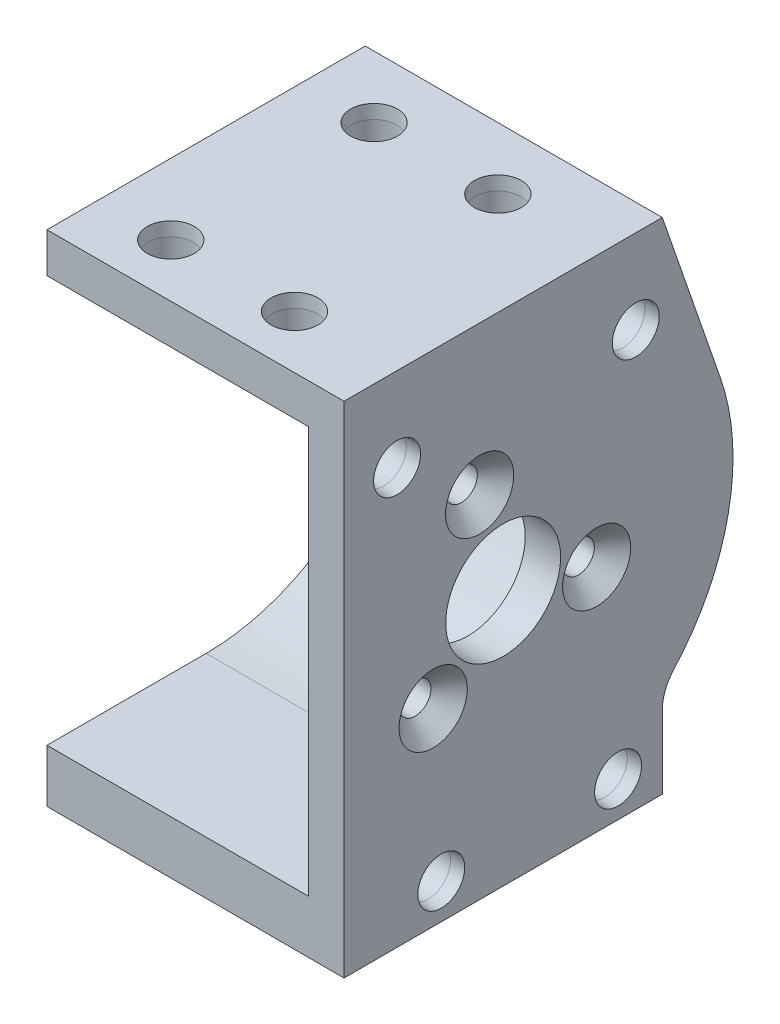
SolidWorks part; units mm, degrees
material "6061 Alloy"
ref_plane "Front Plane" through (0, 0, 0) normal (0, 0, 1) x (1, 0, 0)
ref_plane "Top Plane" through (0, 0, 0) normal (0, 1, 0) x (1, 0, 0)
ref_plane "Right Plane" through (0, 0, 0) normal (1, 0, 0) x (0, 0, -1)
ref_plane "Motor Face w/ 1.5mm tolerance" through (29.6, 0, 0) normal (1, 0, 0) x (0, 0, -1)
sketch "Motor Shell Profile" plane through (0, 0, 0) normal (1, 0, 0) x (0, 0, -1)
  line L0 (0, 22) -> (-16, 22)
  line L1 (-16, -29) -> (18, -29)
  line L2 (-16, 22) -> (-16, 27.5)
  line L3 (-16, 27.5) -> (18, 27.5)
  line L4 (18, -20.7846) -> (18, -29)
  line L5 (0, -22) -> (-16, -22)
  line L6 (-16, -22) -> (-16, -29)
  line L7 (24.5719, 8.4984) -> (18, 27.5)
  arc A0 (0, -22) -> (0, 22) centre (0, 0) ccw
  arc A1 (19.2903, -17.4323) -> (24.5719, 8.4984) centre (0, 0) ccw
  arc A2 (18, -20.7846) -> (19.2903, -17.4323) centre (23, -20.7846) cw
  point P17 (18, -29)
  dimension "D1" = 5.5
  dimension "Motor Diameter" = 22
  dimension "D3" = 26
  dimension "D6" = 5
  dimension "D2" = 7
  dimension "D4" = 16
  dimension "D5" = 34
extrude "Motor Shell" add sketch "Motor Shell Profile" along normal offset from surface (33.6 mm away) 4 up to plane "Motor Face w/ 1.5mm tolerance" offset beyond the face yes
sketch "Sketch3" plane through (29.6, 0, 0) normal (1, 0, 0) x (0, 0, -1)
  line L0 (0, 22) -> (-16, 22)
  line L1 (-16, -22) -> (0, -22)
  line L2 (-16, 22) -> (-16, -22)
  arc A0 (0, 22) -> (0, -22) centre (0, 0) cw
  circle A2 centre (0, 0) radius 11 construction
  arc A3 (0, -22) -> (0, 22) centre (0, 0) ccw construction
  dimension "D1" = 22
extrude "Motor Mount" add sketch "Sketch3" along normal blind 4
hole_wizard "Mounting Hole" positions "Sketch9" profile "Sketch10" countersink size "M3" standard "ANSI Metric" end condition through all
sketch "Sketch9" plane through (33.6, 0, 0) normal (1, 0, 0) x (0, 0, -1)
  line L1 (0, 0) -> (10.5739, -3.032) construction
  line L3 (18, 27.5) -> (-16, 27.5) construction
  point P0 (10.5739, -3.032)
  dimension "D1" = 11
  dimension "D2" = 16
sketch "Sketch10" plane through (33.6, -3.032, -10.5739) normal (0, 1, 0) x (0, 0, -1)
  line L0 (0, 0) -> (0, 33.6)
  line L1 (0, 33.6) -> (1.8, 33.6)
  line L2 (1.8, 33.6) -> (1.8, 2.06)
  line L3 (1.8, 2.06) -> (3.86, 0)
  line L5 (3.86, 0) -> (0, 0)
  line L6 (-1.8, 2.06) -> (-3.86, 0) construction
  line L11 (0, -6.35) -> (0, 107.95) construction
  dimension "Thru Hole Dia." = 3.6
  dimension "Thru Hole Depth" = 33.6
  dimension "Near C'Sink Dia." = 7.72
  dimension "Near C'Sink Angle" = 90
pattern_circular "Hole Duplication" count 3 over 360 about axis through (0, 0, 0) along (1, 0, 0) of "Mounting Hole"
hole_wizard "Mounting Hole up" [suppressed] positions "Sketch28" profile "Sketch29" countersink size "M3" standard "ANSI Metric"
sketch "Sketch28" plane through (33.6, 0, 0) normal (1, 0, 0) x (0, 0, -1)
  line L1 (0, 0) -> (10.5739, 3.032) construction
  line L4 (18, 27.5) -> (-16, 27.5) construction
  point P0 (10.5739, 3.032)
  dimension "D1" = 11
  dimension "D2" = 16
sketch "Sketch29" plane through (33.6, 3.032, -10.5739) normal (0, 1, 0) x (0, 0, -1)
  line L0 (0, 0) -> (0, 33.6)
  line L1 (0, 33.6) -> (1.7, 33.6)
  line L2 (1.7, 33.6) -> (1.7, 2.16)
  line L3 (1.7, 2.16) -> (3.86, 0)
  line L5 (3.86, 0) -> (0, 0)
  line L6 (-1.7, 2.16) -> (-3.86, 0) construction
  line L11 (0, -6.35) -> (0, 107.95) construction
  dimension "Thru Hole Dia." = 3.6
  dimension "Thru Hole Depth" = 33.6
  dimension "Near C'Sink Dia." = 7.72
  dimension "Near C'Sink Angle" = 90
sketch "Sketch11" plane through (33.6, 0, 0) normal (1, 0, 0) x (0, 0, -1)
  circle A0 centre (0, 0) radius 6.5
  dimension "D1" = 13
extrude "Shaft Base Cutout" cut sketch "Sketch11" against normal through all
ref_plane "U Joint Base Plane" through (36.1, 0, 0) normal (1, 0, 0) x (0, 0, -1)
ref_plane "Pin Hole Plane" through (0, 0, 15) normal (0, 0, 1) x (1, 0, 0)
hole_wizard "CSK for M3 Insert SFHCS1" positions "Sketch13" profile "Sketch15" countersink size "M3 Insert" standard "ANSI Metric"
sketch "Sketch13" plane through (33.6, 0, 0) normal (1, 0, 0) x (0, 0, -1)
  point P0 (-7, -25)
  point P2 (13, -25)
  point P9 (-12, 18)
  point P11 (15, 18)
  dimension "D1" = 20
  dimension "D2" = 25
  dimension "D3" = 7
  dimension "D4" = 18
  dimension "D5" = 27
  dimension "D6" = 15
sketch "Sketch15" plane through (33.6, -25, 7) normal (0, 1, 0) x (0, 0, -1)
  line L0 (0, 0) -> (0, 3.8)
  line L1 (0, 3.8) -> (2.55, 3.8)
  line L2 (2.55, 3.8) -> (2.55, 1.5016)
  line L3 (2.55, 1.5016) -> (2.655, 0)
  line L5 (2.655, 0) -> (0, 0)
  line L6 (-2.55, 1.5016) -> (-2.655, 0) construction
  line L10 (0, 3.8) -> (-2.55, 3.8) construction
  line L11 (0, -6.35) -> (0, 107.95) construction
  dimension "Hole Dia." = 5.1
  dimension "Hole Depth" = 3.8
  dimension "Near C'Sink Dia." = 5.31
  dimension "Near C'Sink Angle" = 8
  dimension "Drill Angle" = 180
hole_wizard "CSK for M3 Insert SFHCS2" positions "Sketch17" profile "Sketch18" countersink size "M3 Insert" standard "ANSI Metric"
sketch "Sketch17" plane through (0, 27.5, 0) normal (0, 1, 0) x (1, 0, 0)
  line L2 (0, 1) -> (38.3988, 1) construction
  line L3 (0, 18) -> (0, -16) construction
  point P0 (22, -12)
  point P2 (8, -12)
  point P17 (8, 11)
  point P19 (22, 11)
  dimension "D1" = 13
  dimension "D2" = 14
  dimension "D3" = 8
  dimension "D4" = 10
sketch "Sketch18" plane through (22, 27.5, 12) normal (1, 0, 0) x (0, 0, 1)
  line L0 (0, 0) -> (0, 3.8)
  line L1 (0, 3.8) -> (2.55, 3.8)
  line L2 (2.55, 3.8) -> (2.55, 1.5016)
  line L3 (2.55, 1.5016) -> (2.655, 0)
  line L5 (2.655, 0) -> (0, 0)
  line L6 (-2.55, 1.5016) -> (-2.655, 0) construction
  line L10 (0, 3.8) -> (-2.55, 3.8) construction
  line L11 (0, -6.35) -> (0, 107.95) construction
  dimension "Hole Dia." = 5.1
  dimension "Hole Depth" = 3.8
  dimension "Near C'Sink Dia." = 5.31
  dimension "Near C'Sink Angle" = 8
  dimension "Drill Angle" = 180
sketch "Sketch25" plane through (0, 0, 0) normal (-1, 0, 0) x (0, 0, 1)
  line L0 (0, 23) -> (16, 23)
  line L1 (16, 27.5) -> (16, 22) construction
  line L2 (0, -23) -> (16, -23)
  line L3 (16, -22) -> (16, -29) construction
  line L4 (16, -23) -> (16, 23)
  arc A0 (0, 23) -> (0, -23) centre (0, 0) ccw
  dimension "D1" = 46
extrude "Cut-Extrude1" cut sketch "Sketch25" against normal up to surface (29.6 mm away) up to face at (29.6, 0, 6.5)
hole_wizard "CSK for M3 Insert SFHCS3" positions "Sketch26" profile "Sketch27" countersink size "M3 Insert" standard "ANSI Metric"
sketch "Sketch26" plane through (0, -29, 0) normal (0, -1, 0) x (-1, 0, 0)
  line L2 (-33.6, 1) -> (5.9299, 1) construction
  line L4 (-33.6, -16) -> (-33.6, 18) construction
  line L5 (0, -16) -> (0, 18) construction
  point P0 (-8, -12)
  point P2 (-22, -12)
  point P17 (-22, 11)
  point P19 (-8, 11)
  point P27 (-33.6, 1)
  dimension "D1" = 13
  dimension "D2" = 14
  dimension "D3" = 8
  dimension "D4" = 10
sketch "Sketch27" plane through (8, -29, 12) normal (1, 0, 0) x (0, 0, -1)
  line L0 (0, 0) -> (0, 3.8)
  line L1 (0, 3.8) -> (2.55, 3.8)
  line L2 (2.55, 3.8) -> (2.55, 1.5016)
  line L3 (2.55, 1.5016) -> (2.655, 0)
  line L5 (2.655, 0) -> (0, 0)
  line L6 (-2.55, 1.5016) -> (-2.655, 0) construction
  line L10 (0, 3.8) -> (-2.55, 3.8) construction
  line L11 (0, -6.35) -> (0, 107.95) construction
  dimension "Hole Dia." = 5.1
  dimension "Hole Depth" = 3.8
  dimension "Near C'Sink Dia." = 5.31
  dimension "Near C'Sink Angle" = 8
  dimension "Drill Angle" = 180
pattern_circular "CirPattern1" [suppressed] count 3 over 360
sketch "Sketch30" plane through (0, 0, 16) normal (0, 0, 1) x (1, 0, 0)
  line L0 (0, 23) -> (29.6, 23)
  line L1 (29.6, 23) -> (29.6, -23)
  line L2 (29.6, -23) -> (0, -23)
  line L3 (0, -23) -> (0, -29) construction
  line L4 (29.6, -23) -> (0, -23) construction
  line L5 (0, -23) -> (0, -29)
  line L6 (0, -29) -> (33.6, -29)
  line L7 (33.6, -29) -> (33.6, 27.5)
  line L8 (33.6, 27.5) -> (0, 27.5)
  line L9 (0, 27.5) -> (0, 23)
extrude "Additional structure" add sketch "Sketch30" along normal blind 2
